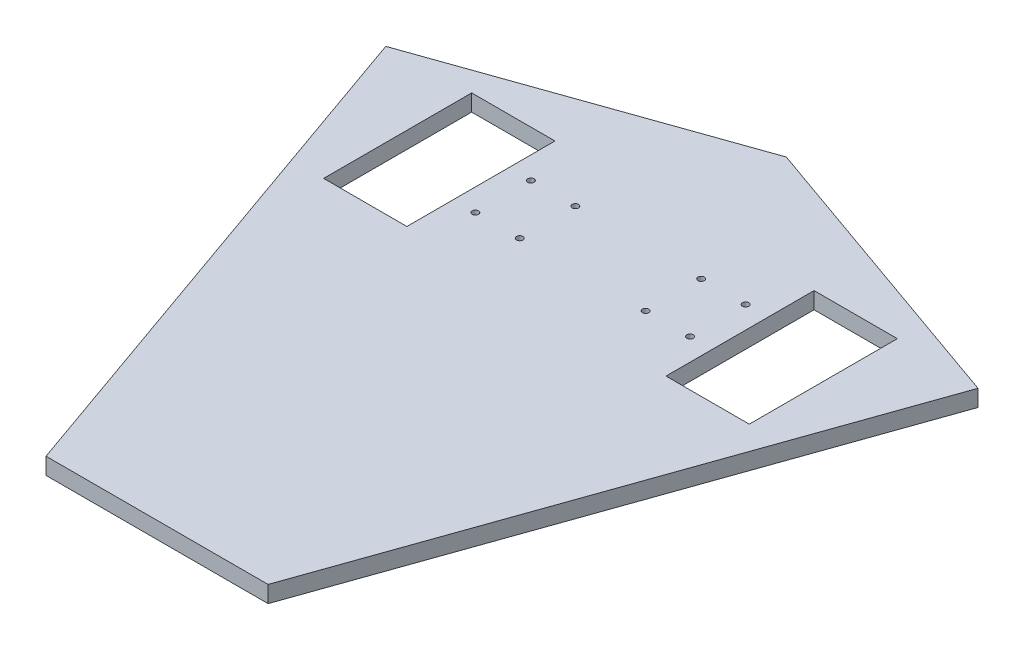
SolidWorks part; units mm, degrees
material "Cèdre"
ref_plane "Plan de face" through (0, 0, 0) normal (0, 0, 1) x (1, 0, 0)
ref_plane "Plan de dessus" through (0, 0, 0) normal (0, 1, 0) x (1, 0, 0)
ref_plane "Plan de droite" through (0, 0, 0) normal (1, 0, 0) x (0, 0, -1)
sketch "Esquisse1" plane through (0, 0, 0) normal (0, 1, 0) x (1, 0, 0)
  line L0 (0, 110) -> (0, -230) construction
  line L1 (0, 110) -> (-160, 53.5782)
  line L2 (-160, 53.5782) -> (-60, -230)
  line L3 (-60, -230) -> (60, -230)
  line L4 (0, 110) -> (160, 53.5782)
  line L5 (160, 53.5782) -> (60, -230)
  dimension "D1" = 160
  dimension "D2" = 110
  dimension "D3" = 230
  dimension "D4" = 60
extrude "Boss.-Extru.1" add sketch "Esquisse1" against normal blind 9
sketch "Esquisse2" plane through (0, 0, 0) normal (0, 1, 0) x (1, 0, 0)
  line L1 (-115, 55) -> (-70, 55)
  line L2 (-115, 55) -> (-115, -25)
  line L3 (-115, -25) -> (-70, -25)
  line L4 (-70, 55) -> (-70, -25)
  dimension "D1" = 80
  dimension "D2" = 55
  dimension "D3" = 45
  dimension "D4" = 70
extrude "Enlèv. mat.-Extru.2" cut sketch "Esquisse2" against normal up to next (9 mm away)
mirror "Symétrie1" about plane through (0, 0, 0) normal (1, 0, 0) of "Enlèv. mat.-Extru.2"
hole_wizard "Dégagement M31" positions "Esquisse3" profile "Esquisse4" hole size "M3" standard "Ansi Metric"
sketch "Esquisse3" plane through (0, 0, 0) normal (0, 1, 0) x (1, 0, 0)
  line L0 (-70, -25) -> (-70, 55) construction
  line L1 (-34, 0) -> (-58, 0) construction
  point P0 (-58, 0)
  point P2 (-34, 0)
  dimension "D1" = 12
  dimension "D2" = 24
  dimension "D3" = 0
sketch "Esquisse4" plane through (-58, 0, 0) normal (1, 0, 0) x (0, 0, 1)
  line L0 (0, 0) -> (0, 11.0215)
  line L1 (0, 11.0215) -> (1.7, 10)
  line L2 (1.7, 10) -> (1.7, 0)
  line L5 (1.7, 0) -> (0, 0)
  line L10 (0, 11.0215) -> (-1.7, 10) construction
  line L11 (0, -6.35) -> (0, 107.95) construction
  dimension "Diamètre du perçage" = 3.4
  dimension "Profondeur du perçage" = 10
  dimension "Angle de pointe" = 118
ref_plane "Plan1" through (0, 0, -15) normal (0, 0, 1) x (1, 0, 0)
mirror "Symétrie2" about plane through (0, 0, -15) normal (0, 0, 1) of "Dégagement M31"
mirror "Symétrie3" about plane through (0, 0, 0) normal (1, 0, 0) of "Symétrie2", "Dégagement M31"
